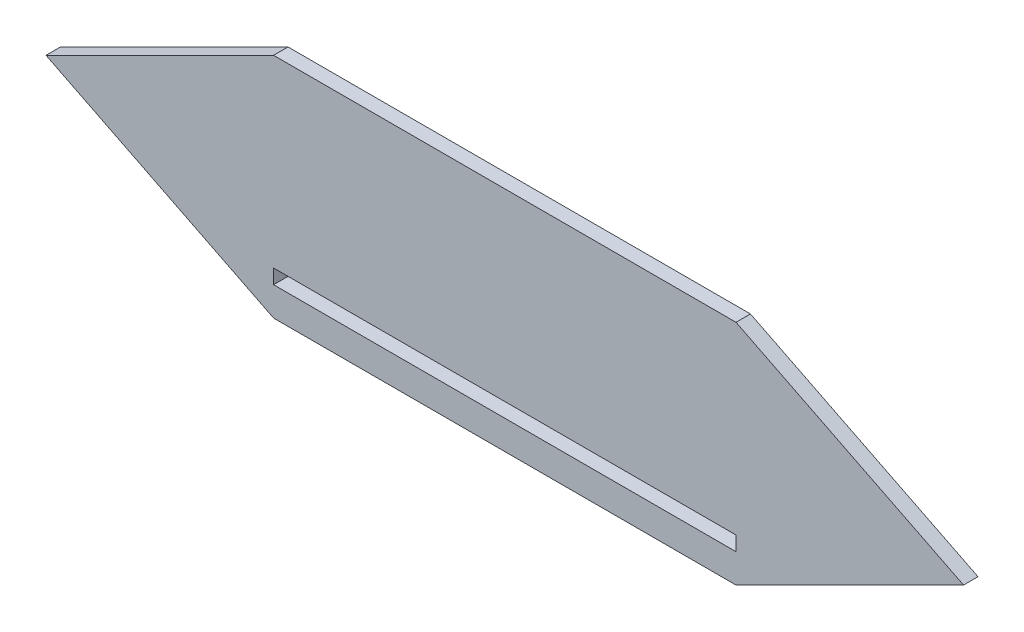
SolidWorks part; units mm, degrees
material "AISI 316 Annealed Stainless Steel Bar (SS)"
ref_plane "Front Plane" through (0, 0, 0) normal (0, 0, 1) x (1, 0, 0)
ref_plane "Top Plane" through (0, 0, 0) normal (0, 1, 0) x (1, 0, 0)
ref_plane "Right Plane" through (0, 0, 0) normal (1, 0, 0) x (0, 0, -1)
sketch "Sketch1" plane through (0, 0, 0) normal (0, 0, 1) x (1, 0, 0)
  line L0 (0, 50) -> (-100, 50) construction
  line L1 (0, 0) -> (203.2, 0)
  line L2 (0, 0) -> (0, 100)
  line L3 (0, 100) -> (203.2, 100)
  line L4 (203.2, 0) -> (203.2, 100)
  line L5 (101.6, 0) -> (101.6, 100) construction
  line L6 (0, 100) -> (-100, 50)
  line L7 (-100, 50) -> (0, 0)
  line L8 (303.2, 50) -> (203.2, 0)
  line L9 (203.2, 100) -> (303.2, 50)
  dimension "D3" = 100
  dimension "D1" = 203.2
  dimension "D2" = 100
extrude "Boss-Extrude1" add sketch "Sketch1" along normal blind 6.35
sketch "Sketch2" plane through (0, 0, 0) normal (0, 0, -1) x (-1, 0, 0)
  line L0 (0, 0) -> (-203.2, 0) construction
  line L5 (-203.2, 6.7) -> (-177.8, 6.7)
  line L6 (-203.2, 6.7) -> (-203.2, 12.7)
  line L7 (-203.2, 12.7) -> (-177.8, 12.7)
  line L8 (-177.8, 6.7) -> (-177.8, 12.7)
  line L9 (6, 25.05) -> (6, 6.7)
  line L10 (-101.6, 0) -> (-101.6, 100) construction
  line L11 (0, 100) -> (-203.2, 100) construction
  line L20 (0, 6.7) -> (6, 6.7)
  line L21 (-203.2, 19.05) -> (-177.8, 19.05)
  line L22 (-203.2, 19.05) -> (-203.2, 25.05)
  line L23 (-203.2, 25.05) -> (-177.8, 25.05)
  line L24 (-177.8, 19.05) -> (-177.8, 25.05)
  line L25 (-203.2, 19.05) -> (-203.2, 12.7)
  line L26 (-203.2, 25.05) -> (-209.2, 25.05)
  line L31 (-203.2, 25.05) -> (-203.2, 6.7)
  line L36 (-203.2, 6.7) -> (-209.2, 6.7)
  line L37 (-209.2, 25.05) -> (-209.2, 6.7)
  line L38 (0, 25.05) -> (0, 6.7)
  line L39 (0, 25.05) -> (6, 25.05)
  line L40 (0, 19.05) -> (0, 12.7)
  line L41 (-25.4, 19.05) -> (-25.4, 25.05)
  line L50 (0, 25.05) -> (-25.4, 25.05)
  line L51 (0, 19.05) -> (0, 25.05)
  line L52 (0, 19.05) -> (-25.4, 19.05)
  line L53 (-25.4, 6.7) -> (-25.4, 12.7)
  line L54 (0, 12.7) -> (-25.4, 12.7)
  line L55 (0, 6.7) -> (0, 12.7)
  line L56 (0, 6.7) -> (-25.4, 6.7)
  dimension "D1" = 25.4
  dimension "D2" = 6.35
  dimension "D3" = 12.7
  dimension "D4" = 6
  dimension "D5" = 6
  dimension "D6" = 6
  dimension "D7" = 101.6
extrude "Boss-Extrude3" add sketch "Sketch2" along normal blind 25
sketch "Sketch3" plane through (0, 0, 0) normal (0, 0, -1) x (-1, 0, 0)
  line L1 (-203.2, 12.7) -> (0, 12.7)
  line L2 (-203.2, 12.7) -> (-203.2, 19.05)
  line L3 (-203.2, 19.05) -> (0, 19.05)
  line L4 (0, 12.7) -> (0, 19.05)
extrude "Cut-Extrude1" cut sketch "Sketch3" against normal blind 10
